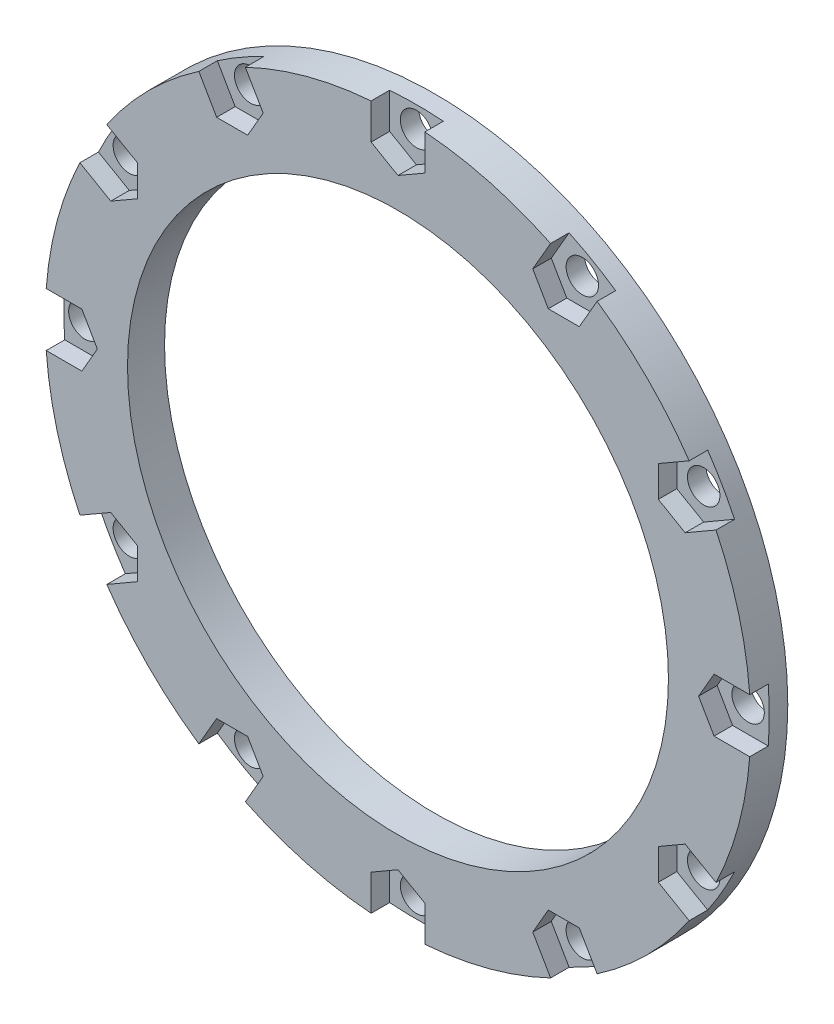
SolidWorks part; units mm, degrees
ref_plane "Front Plane" through (0, 0, 0) normal (0, 0, 1) x (1, 0, 0)
ref_plane "Top Plane" through (0, 0, 0) normal (0, 1, 0) x (1, 0, 0)
ref_plane "Right Plane" through (0, 0, 0) normal (1, 0, 0) x (0, 0, -1)
sketch "Sketch1" plane through (0, 0, 0) normal (0, 0, 1) x (1, 0, 0)
  circle A0 centre (0, 0) radius 38.1
  circle A1 centre (0, 0) radius 29.21
  dimension "D1" = 76.2
  dimension "D2" = 58.42
extrude "Boss-Extrude1" add sketch "Sketch1" along normal blind 4
sketch "Sketch2" plane through (0, 0, 4) normal (0, 0, 1) x (1, 0, 0)
  line L0 (0, 0) -> (0, 44.3901) construction
  circle A0 centre (0, 0) radius 35.814 construction
  circle A1 centre (0, 35.814) radius 1.75
  circle A2 centre (17.907, 31.0158) radius 1.75
  circle A3 centre (31.0158, 17.907) radius 1.75
  circle A4 centre (35.814, 0) radius 1.75
  circle A5 centre (31.0158, -17.907) radius 1.75
  circle A6 centre (17.907, -31.0158) radius 1.75
  circle A7 centre (0, -35.814) radius 1.75
  circle A8 centre (-17.907, -31.0158) radius 1.75
  circle A9 centre (-31.0158, -17.907) radius 1.75
  circle A10 centre (-35.814, 0) radius 1.75
  circle A11 centre (-31.0158, 17.907) radius 1.75
  circle A12 centre (-17.907, 31.0158) radius 1.75
  point P30 (0, 0)
  dimension "D1" = 71.628
  dimension "D2" = 3.5
  dimension "D3" = 12
extrude "Cut-Extrude1" cut sketch "Sketch2" against normal through all
sketch "Sketch3" plane through (0, 0, 4) normal (0, 0, 1) x (1, 0, 0)
  line L0 (0, 0) -> (0, 45.6158) construction
  line L1 (-2.9, 37.9895) -> (0, 39.1626)
  line L2 (16.4833, 34.3498) -> (19.5813, 33.9158)
  line L3 (-2.9, 37.9895) -> (-2.9, 34.1397)
  line L4 (-2.9, 34.1397) -> (0, 32.4654)
  line L5 (0, 32.4654) -> (2.9, 34.1397)
  line L6 (2.9, 34.1397) -> (2.9, 37.9895)
  line L7 (16.4833, 34.3498) -> (14.5584, 31.0158)
  line L8 (2.9, 37.9895) -> (0, 39.1626)
  line L9 (14.5584, 31.0158) -> (16.2327, 28.1158)
  line L10 (16.2327, 28.1158) -> (19.5813, 28.1158)
  line L11 (19.5813, 28.1158) -> (21.5062, 31.4498)
  line L12 (21.5062, 31.4498) -> (19.5813, 33.9158)
  line L13 (31.4498, 21.5062) -> (33.9158, 19.5813)
  line L14 (31.4498, 21.5062) -> (28.1158, 19.5813)
  line L15 (28.1158, 19.5813) -> (28.1158, 16.2327)
  line L16 (28.1158, 16.2327) -> (31.0158, 14.5584)
  line L17 (31.0158, 14.5584) -> (34.3498, 16.4833)
  line L18 (34.3498, 16.4833) -> (33.9158, 19.5813)
  line L19 (37.9895, 2.9) -> (39.1626, 0)
  line L20 (37.9895, 2.9) -> (34.1397, 2.9)
  line L21 (34.1397, 2.9) -> (32.4654, 0)
  line L22 (32.4654, 0) -> (34.1397, -2.9)
  line L23 (34.1397, -2.9) -> (37.9895, -2.9)
  line L24 (37.9895, -2.9) -> (39.1626, 0)
  line L25 (34.3498, -16.4833) -> (33.9158, -19.5813)
  line L26 (34.3498, -16.4833) -> (31.0158, -14.5584)
  line L27 (31.0158, -14.5584) -> (28.1158, -16.2327)
  line L28 (28.1158, -16.2327) -> (28.1158, -19.5813)
  line L29 (28.1158, -19.5813) -> (31.4498, -21.5062)
  line L30 (31.4498, -21.5062) -> (33.9158, -19.5813)
  line L31 (21.5062, -31.4498) -> (19.5813, -33.9158)
  line L32 (21.5062, -31.4498) -> (19.5813, -28.1158)
  line L33 (19.5813, -28.1158) -> (16.2327, -28.1158)
  line L34 (16.2327, -28.1158) -> (14.5584, -31.0158)
  line L35 (14.5584, -31.0158) -> (16.4833, -34.3498)
  line L36 (16.4833, -34.3498) -> (19.5813, -33.9158)
  line L37 (2.9, -37.9895) -> (0, -39.1626)
  line L38 (2.9, -37.9895) -> (2.9, -34.1397)
  line L39 (2.9, -34.1397) -> (0, -32.4654)
  line L40 (0, -32.4654) -> (-2.9, -34.1397)
  line L41 (-2.9, -34.1397) -> (-2.9, -37.9895)
  line L42 (-2.9, -37.9895) -> (0, -39.1626)
  line L43 (-16.4833, -34.3498) -> (-19.5813, -33.9158)
  line L44 (-16.4833, -34.3498) -> (-14.5584, -31.0158)
  line L45 (-14.5584, -31.0158) -> (-16.2327, -28.1158)
  line L46 (-16.2327, -28.1158) -> (-19.5813, -28.1158)
  line L47 (-19.5813, -28.1158) -> (-21.5062, -31.4498)
  line L48 (-21.5062, -31.4498) -> (-19.5813, -33.9158)
  line L49 (-31.4498, -21.5062) -> (-33.9158, -19.5813)
  line L50 (-31.4498, -21.5062) -> (-28.1158, -19.5813)
  line L51 (-28.1158, -19.5813) -> (-28.1158, -16.2327)
  line L52 (-28.1158, -16.2327) -> (-31.0158, -14.5584)
  line L53 (-31.0158, -14.5584) -> (-34.3498, -16.4833)
  line L54 (-34.3498, -16.4833) -> (-33.9158, -19.5813)
  line L55 (-37.9895, -2.9) -> (-39.1626, 0)
  line L56 (-37.9895, -2.9) -> (-34.1397, -2.9)
  line L57 (-34.1397, -2.9) -> (-32.4654, 0)
  line L58 (-32.4654, 0) -> (-34.1397, 2.9)
  line L59 (-34.1397, 2.9) -> (-37.9895, 2.9)
  line L60 (-37.9895, 2.9) -> (-39.1626, 0)
  line L61 (-34.3498, 16.4833) -> (-33.9158, 19.5813)
  line L62 (-34.3498, 16.4833) -> (-31.0158, 14.5584)
  line L63 (-31.0158, 14.5584) -> (-28.1158, 16.2327)
  line L64 (-28.1158, 16.2327) -> (-28.1158, 19.5813)
  line L65 (-28.1158, 19.5813) -> (-31.4498, 21.5062)
  line L66 (-31.4498, 21.5062) -> (-33.9158, 19.5813)
  line L67 (-21.5062, 31.4498) -> (-19.5813, 33.9158)
  line L68 (-21.5062, 31.4498) -> (-19.5813, 28.1158)
  line L69 (-19.5813, 28.1158) -> (-16.2327, 28.1158)
  line L70 (-16.2327, 28.1158) -> (-14.5584, 31.0158)
  line L71 (-14.5584, 31.0158) -> (-16.4833, 34.3498)
  line L72 (-16.4833, 34.3498) -> (-19.5813, 33.9158)
  line L139 (0, 39.1626) -> (-1.45, 38.3255) [skipped]
  line L140 (2.9, 37.4883) -> (1.9248, 38.0513) [skipped]
  circle A0 centre (0, 35.814) radius 2.9 construction
  circle A1 centre (0, 0) radius 38.1 construction
  circle A2 centre (17.907, 31.0158) radius 2.9 construction
  circle A3 centre (31.0158, 17.907) radius 2.9 construction
  circle A4 centre (35.814, 0) radius 2.9 construction
  circle A5 centre (31.0158, -17.907) radius 2.9 construction
  circle A6 centre (17.907, -31.0158) radius 2.9 construction
  circle A7 centre (0, -35.814) radius 2.9 construction
  circle A8 centre (-17.907, -31.0158) radius 2.9 construction
  circle A9 centre (-31.0158, -17.907) radius 2.9 construction
  circle A10 centre (-35.814, 0) radius 2.9 construction
  circle A11 centre (-31.0158, 17.907) radius 2.9 construction
  circle A12 centre (-17.907, 31.0158) radius 2.9 construction
  point P103 (0, 0)
  point P105 (0, 0)
  dimension "D1" = 5.8
  dimension "D2" = 12
extrude "Cut-Extrude2" cut sketch "Sketch3" against normal blind 2
